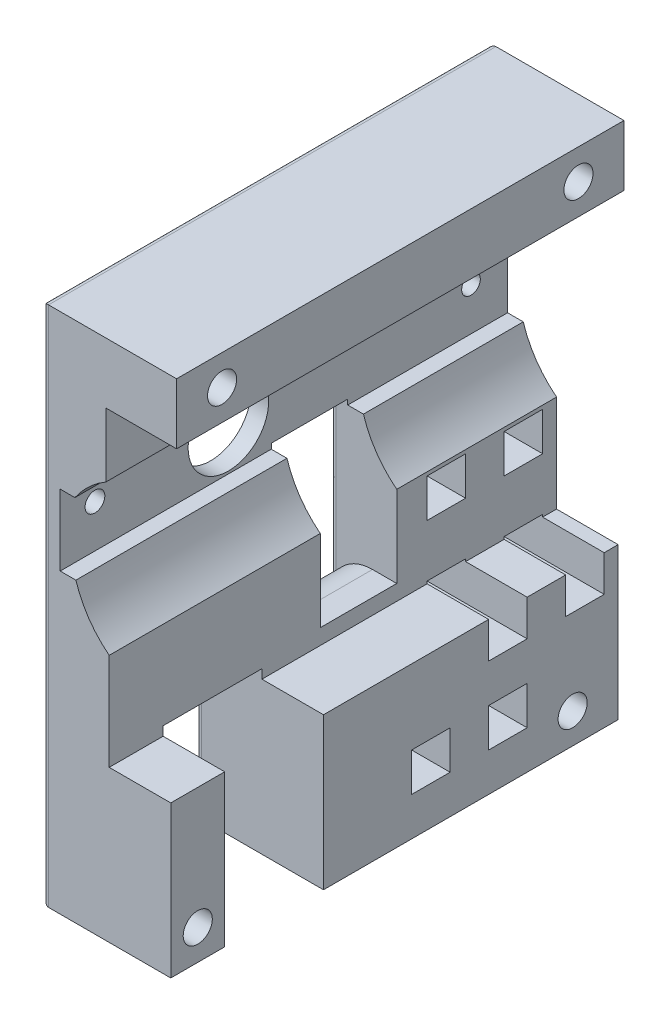
SolidWorks part; units mm, degrees
ref_plane "Front" through (0, 0, 0) normal (0, 0, 1) x (1, 0, 0)
ref_plane "Top" through (0, 0, 0) normal (0, 1, 0) x (1, 0, 0)
ref_plane "Right" through (0, 0, 0) normal (1, 0, 0) x (0, 0, -1)
sketch "Profile" plane through (0, 0, 0) normal (0, 0, 1) x (1, 0, 0)
  line L0 (9.3013, -54.1947) -> (9.3013, -29.1947)
  line L1 (-11.8487, -54.1947) -> (9.3013, -54.1947)
  line L2 (-11.8487, -54.1947) -> (-11.8487, 31.8453)
  line L3 (-11.8487, 31.8453) -> (10.2613, 31.8453)
  line L4 (10.2613, 21.8453) -> (10.2613, 31.8453)
  line L7 (9.3013, -29.1947) -> (-0.8487, -29.1947)
  line L8 (-0.8487, -29.1947) -> (-0.8487, -13.1966)
  line L10 (10.2613, 21.8453) -> (-1.3887, 21.8453)
  line L11 (-1.3887, 21.8453) -> (-1.3887, 11.2835)
  line L12 (-6.5097, 6.4953) -> (-8.9287, 6.4953)
  line L13 (-8.9287, 6.4953) -> (-8.9287, -5.2047)
  line L14 (-8.9287, -5.2047) -> (-6.3407, -5.2047)
  arc A0 (-6.3407, -5.2047) -> (-0.8487, -13.1966) centre (9.1973, -0.41) ccw
  arc A1 (-6.5097, 6.4953) -> (-1.3887, 11.2835) centre (6.8957, -2.7089) cw
  point P0 (0, 0)
  dimension "D15" = 16.261
  dimension "D16" = 16.261
  dimension "D1" = 86.04
  dimension "D2" = 22.11
  dimension "D3" = 10
  dimension "D4" = 25
  dimension "D5" = 21.15
  dimension "D6" = 10.15
  dimension "D7" = 11.65
  dimension "D8" = 10.5617
  dimension "D9" = 15.9981
  dimension "D10" = 2.588
  dimension "D11" = 11.7
  dimension "D12" = 2.4191
  dimension "D13" = 5.492
  dimension "D14" = 23.99
extrude "ProfileExtrude" add sketch "Profile" along normal blind 73.76
sketch "HoseWindow" plane through (-11.8487, 0, 0) normal (-1, 0, 0) x (0, 0, 1)
  line L0 (73.76, -54.1947) -> (0, -54.1947) construction
  line L1 (64.87, -54.1947) -> (48.58, -54.1947)
  line L2 (64.87, -54.1947) -> (64.87, -27.6947)
  line L3 (64.87, -27.6947) -> (48.58, -27.6947)
  line L4 (48.58, -54.1947) -> (48.58, -27.6947)
  dimension "D1" = 16.29
  dimension "D2" = 26.5
  dimension "D3" = 8.89
extrude "HoseWindowCut" cut sketch "HoseWindow" against normal through all
sketch "CageScrews" plane through (-11.8487, 0, 0) normal (-1, 0, 0) x (0, 0, 1)
  line L0 (73.76, 31.8453) -> (0, 31.8453) construction
  line L1 (0, 31.8453) -> (0, -54.1947) construction
  line L2 (73.76, 31.8453) -> (73.76, -54.1947) construction
  line L3 (73.76, -54.1947) -> (64.87, -54.1947) construction
  line L4 (48.58, -54.1947) -> (0, -54.1947) construction
  circle A0 centre (7.5, 26.8453) radius 2.4
  circle A1 centre (66.26, 26.8453) radius 2.4
  circle A2 centre (7.5, -49.1947) radius 2.4
  circle A3 centre (69.31, -49.1947) radius 2.4
  dimension "D1" = 4.8
  dimension "D2" = 5
  dimension "D3" = 7.5
  dimension "D4" = 7.5
  dimension "D5" = 5
  dimension "D6" = 5
  dimension "D7" = 4.45
  dimension "D8" = 5
  dimension "D9" = 7.5
extrude "CageScrewsCut" cut sketch "CageScrews" against normal through all
sketch "AxleHole" plane through (-11.8487, 0, 0) normal (-1, 0, 0) x (0, 0, 1)
  line L0 (46.03, -4.7837) -> (46.03, 6.7405) construction
  line L1 (47.361, 8.3595) -> (47.361, 6.7405)
  line L2 (47.361, 6.7405) -> (44.699, 6.7405)
  line L3 (44.699, 6.7405) -> (44.699, 8.3595)
  line L5 (48.58, -54.1947) -> (0, -54.1947) construction
  line L6 (0, 31.8453) -> (0, -54.1947) construction
  line L7 (39.391, 1.8553) -> (52.669, 1.8553) construction
  arc A0 (44.699, 8.3595) -> (47.361, 8.3595) centre (46.03, 1.8553) ccw
  dimension "D1" = 13.278
  dimension "D2" = 1.331
  dimension "D3" = 1.619
  dimension "D4" = 1.619
  dimension "D5" = 46.03
  dimension "D6" = 56.05
extrude "AxleHoleCut" cut sketch "AxleHole" against normal through all
sketch "SetScrewHoles" plane through (-11.8487, 0, 0) normal (-1, 0, 0) x (0, 0, 1)
  line L0 (47.361, 6.7405) -> (44.699, 6.7405) construction
  circle A0 centre (6.03, 1.8553) radius 1.5394
  circle A1 centre (68.03, 1.8553) radius 1.629
  point P6 (46.03, 6.7405)
  point P7 (46.03, 6.7405)
  dimension "D1" = 22
  dimension "D2" = 40
extrude "SetScrewHolesCut" cut sketch "SetScrewHoles" against normal through all
sketch "VelocityWindow" plane through (-11.8487, 0, 0) normal (-1, 0, 0) x (0, 0, 1)
  line L0 (73.76, 31.8453) -> (73.76, -54.1947) construction
  line L1 (38.96, -26.6447) -> (26.35, -26.6447)
  line L2 (38.96, -26.6447) -> (38.96, -4.3547)
  line L3 (38.96, -4.3547) -> (26.35, -4.3547)
  line L4 (26.35, -26.6447) -> (26.35, -4.3547)
  line L5 (38.96, -26.6447) -> (26.35, -4.3547) construction
  line L6 (38.96, -4.3547) -> (26.35, -26.6447) construction
  line L7 (48.58, -54.1947) -> (0, -54.1947) construction
  point P0 (32.655, -15.4997)
  dimension "D1" = 12.61
  dimension "D2" = 22.29
  dimension "D3" = 34.8
  dimension "D4" = 27.55
extrude "VelocityWindowCut" cut sketch "VelocityWindow" against normal through all
fillet "Fillet3" radius 7 1 edges at (-11.8487, -26.6447, 32.655)
sketch "TriggerRackSlotCut" plane through (-11.8487, 0, 0) normal (-1, 0, 0) x (0, 0, 1)
  line L0 (15, -41.4947) -> (21.35, -41.4947)
  line L1 (15, -41.4947) -> (15, -47.8447)
  line L2 (21.35, -41.4947) -> (21.35, -47.8447)
  line L3 (15, -47.8447) -> (21.35, -47.8447)
  line L4 (0, 31.8453) -> (0, -54.1947) construction
  line L5 (27.7, -41.4947) -> (34.05, -41.4947)
  line L6 (34.05, -41.4947) -> (34.05, -47.8447)
  line L7 (27.7, -47.8447) -> (34.05, -47.8447)
  line L8 (27.7, -41.4947) -> (27.7, -47.8447)
  line L9 (8.65, -28.7947) -> (8.65, -35.1447)
  line L10 (2.3, -28.7947) -> (8.65, -28.7947)
  line L11 (2.3, -28.7947) -> (2.3, -35.1447)
  line L12 (2.3, -35.1447) -> (8.65, -35.1447)
  line L13 (15, -28.7947) -> (21.35, -28.7947)
  line L14 (21.35, -28.7947) -> (21.35, -35.1447)
  line L15 (15, -35.1447) -> (21.35, -35.1447)
  line L16 (48.58, -54.1947) -> (0, -54.1947) construction
  line L17 (15, -28.7947) -> (15, -35.1447)
  line L18 (15, -41.4947) -> (15, -28.7947) construction
  line L19 (27.7, -28.7947) -> (34.05, -28.7947) [skipped]
  line L20 (34.05, -28.7947) -> (34.05, -35.1447) [skipped]
  line L21 (27.7, -35.1447) -> (34.05, -35.1447) [skipped]
  line L22 (27.7, -28.7947) -> (27.7, -35.1447) [skipped]
  line L23 (8.65, -13.7947) -> (8.65, -20.1447)
  line L24 (2.3, -13.7947) -> (8.65, -13.7947)
  line L25 (2.3, -13.7947) -> (2.3, -20.1447)
  line L26 (2.3, -20.1447) -> (8.65, -20.1447)
  line L27 (15, -13.7947) -> (21.35, -13.7947)
  line L28 (21.35, -13.7947) -> (21.35, -20.1447)
  line L29 (15, -20.1447) -> (21.35, -20.1447)
  line L30 (15, -13.7947) -> (15, -20.1447)
  dimension "D1" = 6.35
  dimension "D2" = 15
  dimension "D3" = 6.35
  dimension "D4" = 6.35
  dimension "D7" = 12.7
  dimension "D5" = 2
  dimension "D6" = 2
  dimension "D8" = 2
  dimension "D9" = 2
extrude "RackSlotCut" cut sketch "TriggerRackSlotCut" against normal through all
fillet "Fillet4" radius 1 35 edges at (-11.8487, -16.9697, 15) (-11.8487, -20.1447, 18.175) (-11.8487, -16.9697, 21.35) (-11.8487, -13.7947, 18.175) (-11.8487, -13.7947, 5.475) (-11.8487, -16.9697, 2.3) (-11.8487, -16.9697, 8.65) (-11.8487, -20.1447, 5.475) (-11.8487, -35.1447, 5.475) (-11.8487, -31.9697, 2.3) (-11.8487, -28.7947, 5.475) (-11.8487, -31.9697, 8.65) (-11.8487, -31.9697, 21.35) (-11.8487, -28.7947, 18.175) (-11.8487, -31.9697, 15) (-11.8487, -35.1447, 18.175) (-11.8487, -47.8447, 18.175) (-11.8487, -44.6697, 15) (-11.8487, -41.4947, 18.175) (-11.8487, -44.6697, 21.35) (-11.8487, -44.6697, 27.7) (-11.8487, -47.8447, 30.875) (-11.8487, -44.6697, 34.05) (-11.8487, -41.4947, 30.875) (-11.8487, -18.9997, 38.96) (-11.8487, -4.3547, 32.655) (-11.8487, -18.9997, 26.35) (-11.8487, -11.1747, 0) (-11.8487, -54.1947, 24.29) (-11.8487, -40.9447, 48.58) (-11.8487, -27.6947, 56.725) (-11.8487, -40.9447, 64.87) (-11.8487, -54.1947, 69.315) (-11.8487, -11.1747, 73.76) (-11.8487, 31.8453, 36.88)
equation "\"BottomEdge\"=21.15mm"
equation "\"TopEdge\"=22.11mm"
equation "\"TotalHeight\"=86.04mm"
equation "\"TotalLength\"=73.76mm"
equation "\"ScrewClearance\"=10mm"
equation "\"TopDepth\"= 11.65mm"
equation "\"BottomDepth\"=10.15mm"
equation "\"TopHeight\"=10.56175mm"
equation "\"BottomHeight\"=15.99813mm"
equation "\"TopChannelDepth\"=2.41908mm"
equation "\"BottomChannelDepth\"=2.588mm"
equation "\"ChannelHeight\"=11.7mm"
equation "\"ChanRelHeight\"=23.99mm"
equation "\"ChanRelDepth\"=5.492mm"
equation "\"ChamberRadius\"=16.261mm"
equation "\"CageScrewDiameter\"=4.8mm"
equation "\"SetScrewDiameter\"=3.5mm"
equation "\"AxleRadius\"=6.639mm"
equation "\"KeyHeight\"=1.619mm"
equation "\"KeyWidth\"=2.662mm"
equation "\"HoseWindowWidth\"=16.29mm"
equation "\"HoseWindowHeight\"=26.5mm"
equation "\"HoseWindow-Edge\"=8.89mm"
equation "\"CageScrew-VerticalEdge\"=5.0mm"
equation "\"CageScrew-HorizontalEdge\"=7.5mm"
equation "\"CageScrew-HoseCornerScrewEdge\"=4.45mm"
equation "\"Axle-BottomEdge\"=56.05mm"
equation "\"BackSetScrew-Axel\"=40mm"
equation "\"FrontSetScrew-Axel\"=22mm"
equation "\"VelocityWindow-Backedge\"=34.8mm"
equation "\"velocityWindow-bottomedge\"=27.55mm"
equation "\"VelocityWindowHeight\"=22.29mm"
equation "\"VelocityWindowWidth\"=12.61mm"
equation "\"D11@Profile\"= \"ChannelHeight\""
equation "\"D10@Profile\"= \"BottomChannelDepth\""
equation "\"D12@Profile\"= \"TopChannelDepth\""
equation "\"D8@Profile\" = \"TopHeight\""
equation "\"D9@Profile\"= \"BottomHeight\""
equation "\"D6@Profile\"= \"BottomDepth\""
equation "\"D7@Profile\"= \"TopDepth\""
equation "\"D3@Profile\"= \"ScrewClearance\""
equation "\"ScrewClearanceBottom\"=25mm"
equation "\"D4@Profile\"=\"ScrewClearanceBottom\""
equation "\"D5@Profile\"= \"BottomEdge\""
equation "\"D2@Profile\"= \"TopEdge\""
equation "\"D1@Profile\"= \"TotalHeight\""
equation "\"D13@Profile\"= \"ChanRelDepth\""
equation "\"D14@Profile\"= \"ChanRelHeight\""
equation "\"D15@Profile\"= \"ChamberRadius\""
equation "\"D16@Profile\"= \"ChamberRadius\""
equation "\"D1@ProfileExtrude\"= \"TotalLength\""
equation "\"D3@HoseWindow\"= \"HoseWindow-Edge\""
equation "\"D2@HoseWindow\"= \"HoseWindowHeight\""
equation "\"D1@HoseWindow\"= \"HoseWindowWidth\""
equation "\"D1@CageScrews\"= \"CageScrewDiameter\""
equation "\"D9@CageScrews\" = \"CageScrew-HorizontalEdge\""
equation "\"D7@CageScrews\" = \"CageScrew-HoseCornerScrewEdge\""
equation "\"D4@CageScrews\" = \"CageScrew-HorizontalEdge\""
equation "\"D6@CageScrews\"= \"CageScrew-VerticalEdge\""
equation "\"D5@CageScrews\"= \"CageScrew-VerticalEdge\""
equation "\"D8@CageScrews\"= \"CageScrew-VerticalEdge\""
equation "\"D2@CageScrews\"= \"CageScrew-VerticalEdge\""
equation "\"D1@AxleHole\"= \"AxleRadius\" * 2"
equation "\"D4@AxleHole\"= \"KeyHeight\""
equation "\"D3@AxleHole\"= \"KeyHeight\""
equation "\"D2@AxleHole\"= \"KeyWidth\" / 2"
equation "\"Axle-FrontEdge\"=46.03mm"
equation "\"D6@AxleHole\"= \"Axle-BottomEdge\""
equation "\"D5@AxleHole\"= \"Axle-FrontEdge\""
equation "\"D2@SetScrewHoles\"= \"BackSetScrew-Axel\""
equation "\"D1@SetScrewHoles\"= \"FrontSetScrew-Axel\""
equation "\"D1@VelocityWindow\"= \"VelocityWindowWidth\""
equation "\"D2@VelocityWindow\"= \"VelocityWindowHeight\""
equation "\"D3@VelocityWindow\"= \"VelocityWindow-Backedge\""
equation "\"D4@VelocityWindow\"= \"velocityWindow-bottomedge\""
equation "\"bottomslotheight\"=6.35mm"
equation "\"D1@TriggerRackSlotCut\"=\"bottomslotheight\""
equation "\"FrontSlotDepth\"=15mm"
equation "\"SlotSize\"=6.35mm"
equation "\"D3@TriggerRackSlotCut\"=\"SlotSize\""
equation "\"D4@TriggerRackSlotCut\"=\"SlotSize\""
equation "\"D2@TriggerRackSlotCut\"=\"FrontSlotDepth\""
